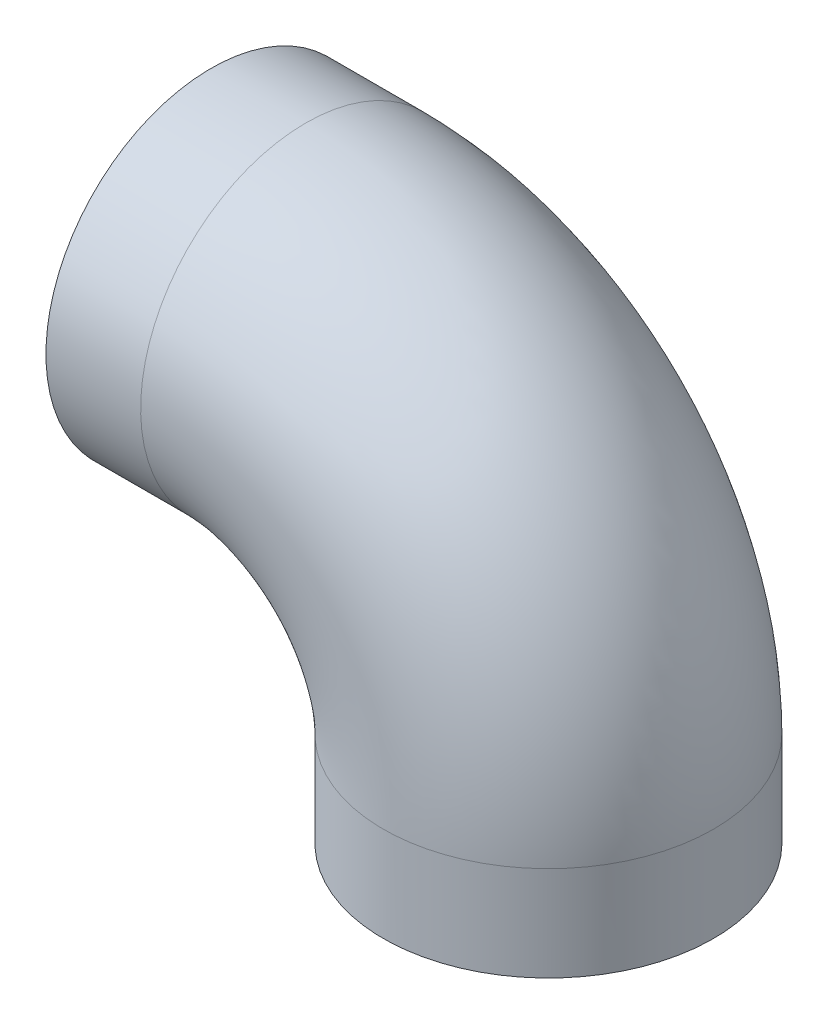
SolidWorks part; units mm, degrees
material "PVC Rigid"
ref_plane "Front Plane" through (0, 0, 0) normal (0, 0, 1) x (1, 0, 0)
ref_plane "Top Plane" through (0, 0, 0) normal (0, 1, 0) x (1, 0, 0)
ref_plane "Right Plane" through (0, 0, 0) normal (1, 0, 0) x (0, 0, -1)
sketch "Sketch1" plane through (0, 0, 0) normal (1, 0, 0) x (0, 0, -1)
  circle A0 centre (0, 0) radius 88.5571
  circle A1 centre (0, 0) radius 72.5043
  dimension "D1" = 16.0528
  dimension "D2" = 145.0086
sketch "Sketch2" plane through (0, 0, 0) normal (0, 0, 1) x (1, 0, 0)
  line L0 (0, 0) -> (50.8, 0)
  line L1 (180.975, -130.175) -> (180.975, -180.975)
  line L4 (0, 0) -> (0, -65.0875) construction
  arc A0 (180.975, -130.175) -> (50.8, 0) centre (50.8, -130.175) ccw
  dimension "D1" = 130.175
  dimension "D2" = 50.8
sweep "Sweep1" add profiles "Sketch1" path "Sketch2"
sketch "Sketch3" plane through (0, -180.975, 0) normal (0, -1, 0) x (-1, 0, 0)
  circle A0 centre (-180.975, 0) radius 84.1375
  dimension "D1" = 168.275
extrude "Cut-Extrude1" cut sketch "Sketch3" against normal blind 44.45 contours A0
sketch "Sketch4" plane through (0, 0, 0) normal (-1, 0, 0) x (0, 0, 1)
  circle A0 centre (0, 0) radius 84.1375
  dimension "D1" = 168.275
extrude "Cut-Extrude2" cut sketch "Sketch4" against normal blind 44.45
